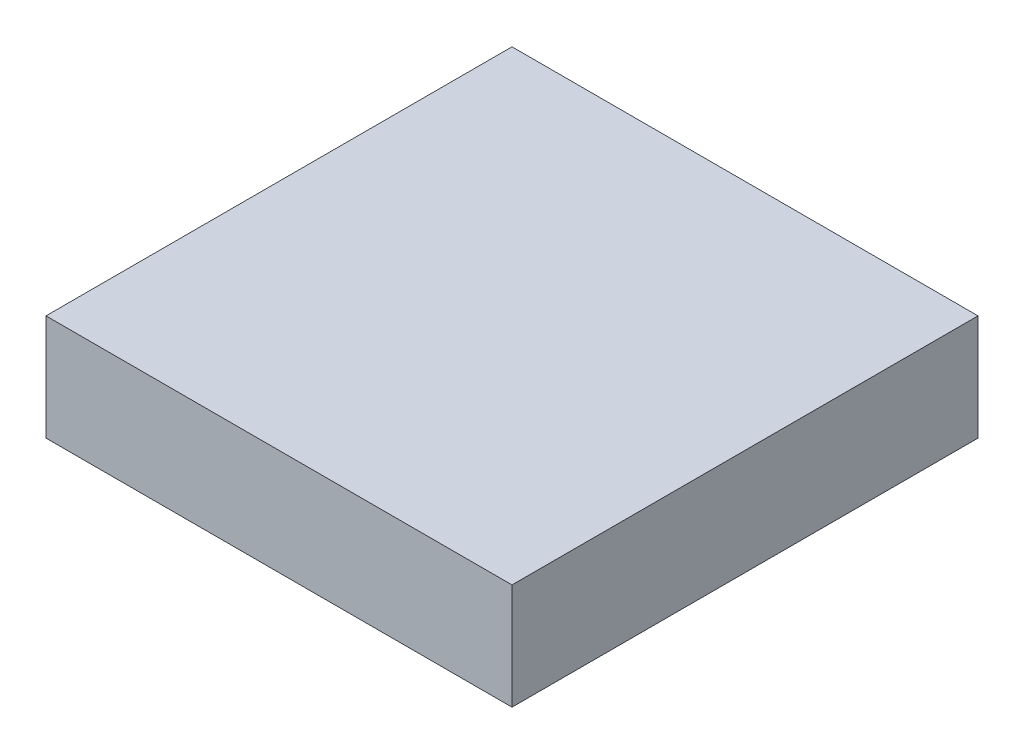
SolidWorks part; units mm, degrees
ref_plane "Front Plane" through (0, 0, 0) normal (0, 0, 1) x (1, 0, 0)
ref_plane "Top Plane" through (0, 0, 0) normal (0, 1, 0) x (1, 0, 0)
ref_plane "Right Plane" through (0, 0, 0) normal (1, 0, 0) x (0, 0, -1)
sketch "Sketch1" plane through (0, 0, 0) normal (0, 1, 0) x (1, 0, 0)
  line L1 (-27.94, -27.94) -> (27.94, -27.94)
  line L2 (-27.94, -27.94) -> (-27.94, 27.94)
  line L3 (-27.94, 27.94) -> (27.94, 27.94)
  line L4 (27.94, -27.94) -> (27.94, 27.94)
  line L5 (-27.94, -27.94) -> (27.94, 27.94) construction
  line L6 (-27.94, 27.94) -> (27.94, -27.94) construction
  point P0 (0, 0)
  dimension "D1" = 55.88
  dimension "D2" = 55.88
extrude "Boss-Extrude1" add sketch "Sketch1" along normal mid plane 12.7
